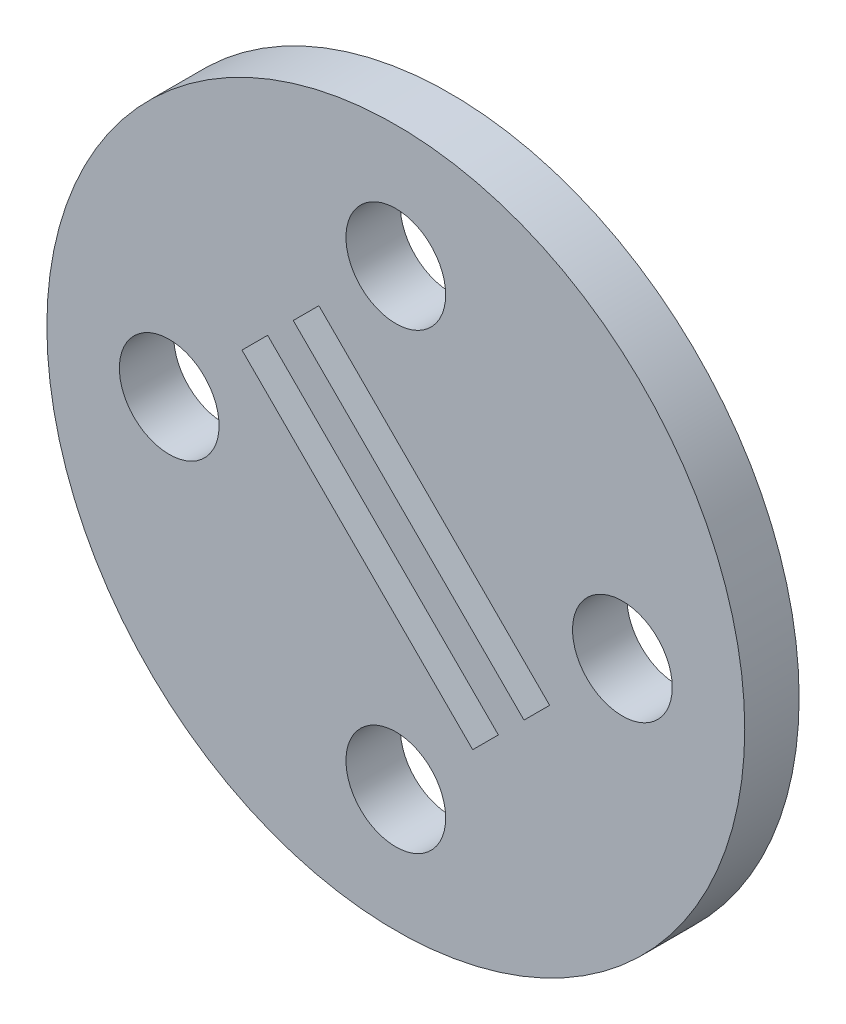
SolidWorks part; units mm, degrees
material "Acrylic (Medium-high impact)"
ref_plane "Front Plane" through (0, 0, 0) normal (0, 0, 1) x (1, 0, 0)
ref_plane "Top Plane" through (0, 0, 0) normal (0, 1, 0) x (1, 0, 0)
ref_plane "Right Plane" through (0, 0, 0) normal (1, 0, 0) x (0, 0, -1)
sketch "Model" plane through (0, 0, 0) normal (0, 0, 1) x (1, 0, 0)
  line L1 (-16.9706, 8.4853) -> (-14.1421, 11.3137)
  line L2 (8.4853, -16.9706) -> (-16.9706, 8.4853)
  line L3 (-11.3137, 14.1421) -> (14.1421, -11.3137)
  line L4 (11.3137, -14.1421) -> (8.4853, -16.9706)
  line L5 (14.1421, -11.3137) -> (16.9706, -8.4853)
  line L6 (16.9706, -8.4853) -> (-8.4853, 16.9706)
  line L7 (-8.4853, 16.9706) -> (-11.3137, 14.1421)
  line L8 (-14.1421, 11.3137) -> (11.3137, -14.1421)
  circle A5 centre (0, 0) radius 38.5
  circle A10 centre (-25, 0) radius 5.5
  circle A11 centre (0, 25) radius 5.5
  circle A12 centre (0, -25) radius 5.5
  circle A13 centre (25, 0) radius 5.5
  dimension "D1" = 11
  dimension "D2" = 77
  dimension "D3" = 8.4853
  dimension "D4" = 11.3137
  dimension "D5" = 14.1421
  dimension "D6" = 8.4853
  dimension "D7" = 25
  dimension "D8" = 8.4853
  dimension "D9" = 11.3137
  dimension "D18" = 25
  dimension "D12" = 25
  dimension "D13" = 25
extrude "Boss-Extrude1" add sketch "Model" along normal blind 6
